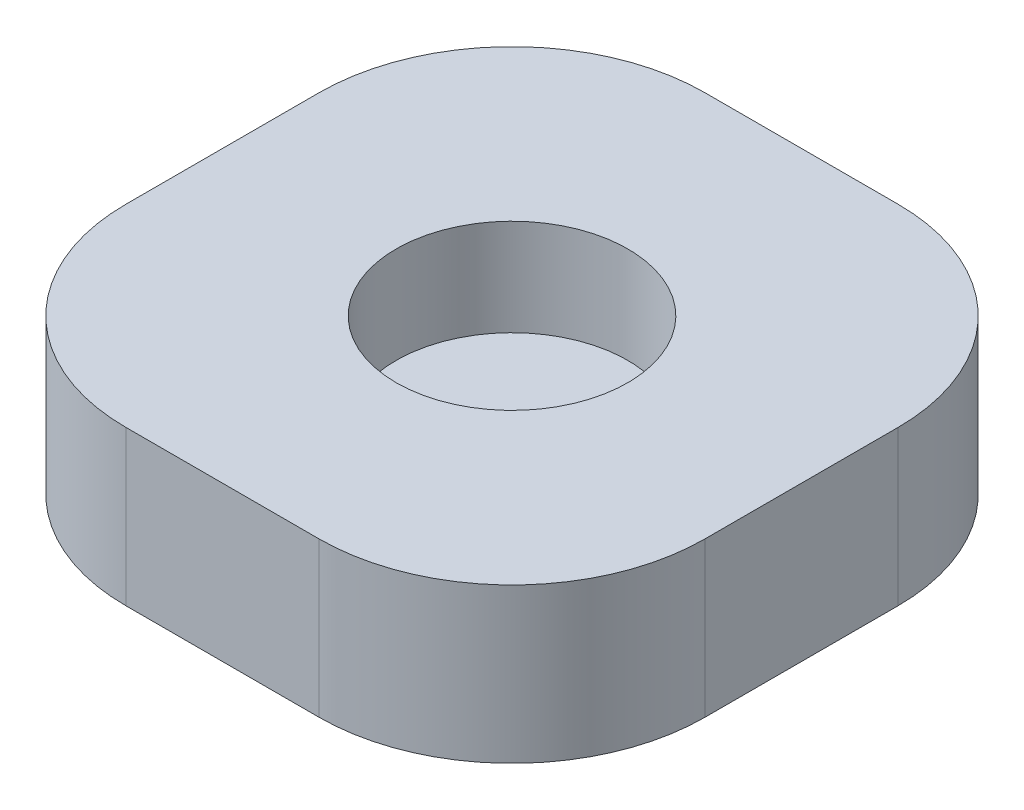
SolidWorks part; units mm, degrees
ref_plane "Front Plane" through (0, 0, 0) normal (0, 0, 1) x (1, 0, 0)
ref_plane "Top Plane" through (0, 0, 0) normal (0, 1, 0) x (1, 0, 0)
ref_plane "Right Plane" through (0, 0, 0) normal (1, 0, 0) x (0, 0, -1)
sketch "Sketch1" plane through (0, 0, 0) normal (0, 1, 0) x (1, 0, 0)
  line L1 (-2.5, -7.5) -> (2.5, -7.5)
  line L2 (-7.5, -2.5) -> (-7.5, 2.5)
  line L3 (-2.5, 7.5) -> (2.5, 7.5)
  line L4 (7.5, -2.5) -> (7.5, 2.5)
  line L5 (-7.5, -7.5) -> (7.5, 7.5) construction
  line L6 (-7.5, 7.5) -> (7.5, -7.5) construction
  arc A1 (2.5, -7.5) -> (7.5, -2.5) centre (2.5, -2.5) ccw
  arc A2 (-2.5, -7.5) -> (-7.5, -2.5) centre (-2.5, -2.5) cw
  arc A3 (-7.5, 2.5) -> (-2.5, 7.5) centre (-2.5, 2.5) cw
  arc A4 (2.5, 7.5) -> (7.5, 2.5) centre (2.5, 2.5) cw
  point P17 (0, 0)
  dimension "D1" = 5
  dimension "D2" = 15
  dimension "D3" = 15
extrude "Boss-Extrude1" add sketch "Sketch1" along normal blind 4
sketch "Sketch2" plane through (0, 4, 0) normal (0, 1, 0) x (1, 0, 0)
  circle A0 centre (0, 0) radius 3
  dimension "D1" = 6
extrude "Cut-Extrude1" cut sketch "Sketch2" against normal blind 2.5
